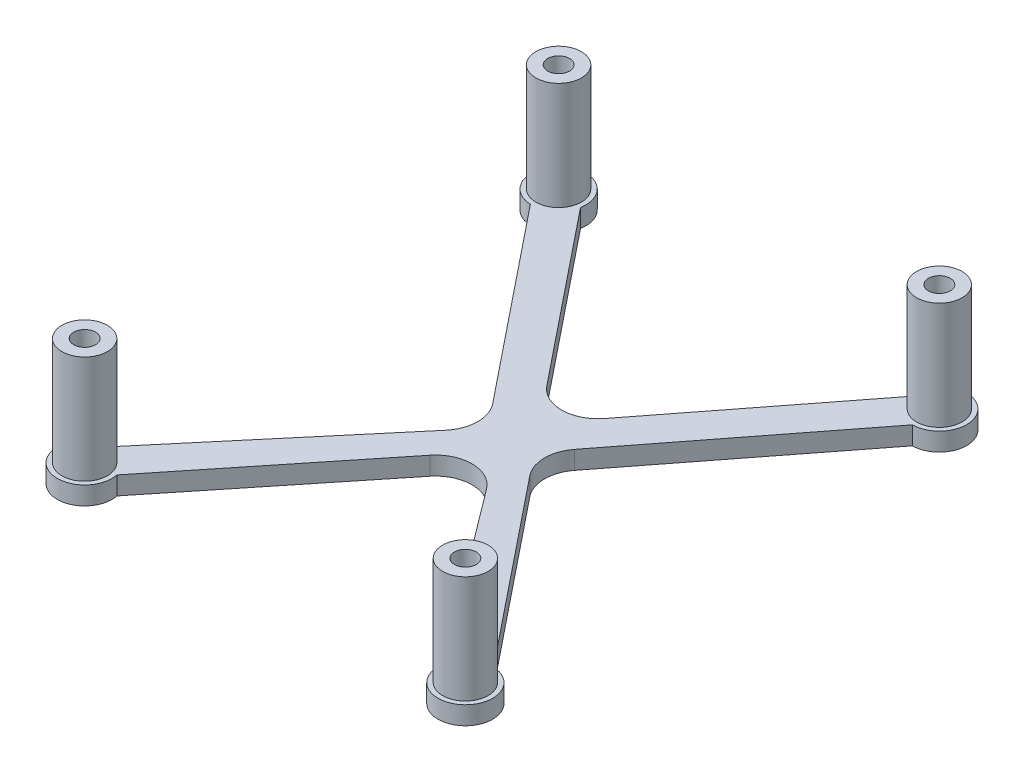
SolidWorks part; units mm, degrees
ref_plane "Front Plane" through (0, 0, 0) normal (0, 0, 1) x (1, 0, 0)
ref_plane "Top Plane" through (0, 0, 0) normal (0, 1, 0) x (1, 0, 0)
ref_plane "Right Plane" through (0, 0, 0) normal (1, 0, 0) x (0, 0, -1)
sketch "Sketch1" plane through (0, -15, 0) normal (0, -1, 0) x (1, 0, 0)
  line L0 (-148.7387, 44.0162) -> (-100.7387, 44.0162) construction
  line L1 (-148.7387, 74.5162) -> (-148.7387, 13.5162) construction
  line L2 (-124.7387, 74.5162) -> (-124.7387, 40.5168) construction
  line L3 (-100.7387, 74.5162) -> (-148.7387, 74.5162) construction
  line L5 (-118.6806, 47.5889) -> (-98.0691, 73.2484)
  line L8 (-130.0173, 47.9647) -> (-151.3305, 73.2466)
  line L9 (-100.7387, 13.5162) -> (-100.7387, 74.5162) construction
  line L10 (-120.0872, 52.216) -> (-101.9448, 76.3616)
  line L11 (-98.1987, 77.0562) -> (-151.2787, 10.9762) construction
  line L12 (-151.2787, 77.0562) -> (-98.1987, 10.9762) construction
  line L13 (-101.9299, 11.7471) -> (-120.3718, 35.4929)
  line L16 (-98.1468, 14.7859) -> (-118.7322, 41.2916)
  line L17 (-99.7749, 9.7101) -> (-148.2042, 76.2635) construction
  line L18 (-151.1675, 73.8832) -> (-96.6224, 12.2424) construction
  line L19 (-151.4082, 14.784) -> (-129.9408, 41.5091)
  line L22 (-149.3408, 9.4196) -> (-128.3444, 35.5583)
  line L23 (-152.5706, 12.014) -> (-97.9261, 73.6222) construction
  line L24 (-100.9648, 76.0631) -> (-149.3408, 9.4196) construction
  line L26 (-128.1091, 52.0862) -> (-147.5475, 76.2854)
  arc A0 (-147.5475, 76.2854) -> (-151.3305, 73.2466) centre (-151.2787, 77.0562) ccw
  arc A1 (-147.5325, 11.6708) -> (-151.4082, 14.784) centre (-151.2787, 10.9762) cw
  arc A2 (-101.9299, 11.7471) -> (-98.1468, 14.7859) centre (-98.1987, 10.9762) ccw
  arc A3 (-101.9448, 76.3616) -> (-98.0691, 73.2484) centre (-98.1987, 77.0562) cw
  arc A4 (-128.1091, 52.0862) -> (-120.0872, 52.216) centre (-124.1486, 55.2676) ccw
  arc A5 (-129.9408, 41.5091) -> (-130.0173, 47.9647) centre (-133.9013, 44.6904) ccw
  arc A6 (-118.7322, 41.2916) -> (-118.6806, 47.5889) centre (-114.7201, 44.4076) cw
  arc A7 (-120.3718, 35.4929) -> (-128.3444, 35.5583) centre (-124.3839, 32.377) ccw
  point P20 (-124.7387, 44.0162)
  point P21 (-124.4157, 43.7568)
  dimension "D1" = 7.62
  dimension "D5" = 5.08
  dimension "D6" = 5.08
  dimension "D7" = 5.08
  dimension "D8" = 5.08
  dimension "D2" = 2.54
  dimension "D3" = 2.54
  dimension "D4" = 2.54
extrude "Boss-Extrude1" add sketch "Sketch1" along normal blind 2.54
sketch "Sketch2" plane through (0, -15, 0) normal (0, 1, 0) x (1, 0, 0)
  circle A0 centre (-98.1987, -10.9762) radius 3.175
  circle A1 centre (-151.2787, -10.9762) radius 3.175
  circle A2 centre (-151.2787, -77.0562) radius 3.175
  circle A3 centre (-98.1987, -77.0562) radius 3.175
extrude "Boss-Extrude2" add sketch "Sketch2" along normal up to surface (15 mm away)
hole_wizard "CBORE for #00 Binding Head Machine Screw1" positions "Sketch4" profile "Sketch5" counterbore size "#00" standard "ANSI Inch" end condition through all
sketch "Sketch4" plane through (0, -17.54, 0) normal (0, -1, 0) x (-1, 0, 0)
  point P0 (151.2787, -10.9762)
sketch "Sketch5" plane through (-151.2787, -17.54, 10.9762) normal (1, 0, 0) x (0, 0, -1)
  line L0 (0, 0) -> (0, 17.54)
  line L1 (0, 17.54) -> (1.524, 17.54)
  line L3 (1.524, 17.54) -> (1.524, 5.08)
  line L4 (1.524, 5.08) -> (2.8575, 5.08)
  line L5 (2.8575, 5.08) -> (2.8575, 0)
  line L7 (2.8575, 0) -> (0, 0)
  line L11 (0, -6.35) -> (0, 107.95) construction
  dimension "Thru Hole Dia." = 3.048
  dimension "Thru Hole Depth" = 17.54
  dimension "C'Bore Dia." = 5.715
  dimension "C'Bore Depth" = 5.08
hole_wizard "CBORE for #00 Binding Head Machine Screw2" positions "Sketch10" profile "Sketch9" counterbore size "#00" standard "ANSI Inch" end condition through all
sketch "Sketch10" plane through (0, -17.54, 0) normal (0, -1, 0) x (-1, 0, 0)
  point P0 (98.1987, -10.9762)
  point P3 (98.1987, -77.0562)
  point P6 (151.2787, -77.0562)
sketch "Sketch9" plane through (-98.1987, -17.54, 10.9762) normal (1, 0, 0) x (0, 0, -1)
  line L0 (0, 0) -> (0, 17.54)
  line L1 (0, 17.54) -> (1.524, 17.54)
  line L3 (1.524, 17.54) -> (1.524, 5.08)
  line L4 (1.524, 5.08) -> (2.8575, 5.08)
  line L5 (2.8575, 5.08) -> (2.8575, 0)
  line L7 (2.8575, 0) -> (0, 0)
  line L11 (0, -6.35) -> (0, 107.95) construction
  dimension "Thru Hole Dia." = 3.048
  dimension "Thru Hole Depth" = 17.54
  dimension "C'Bore Dia." = 5.715
  dimension "C'Bore Depth" = 5.08
